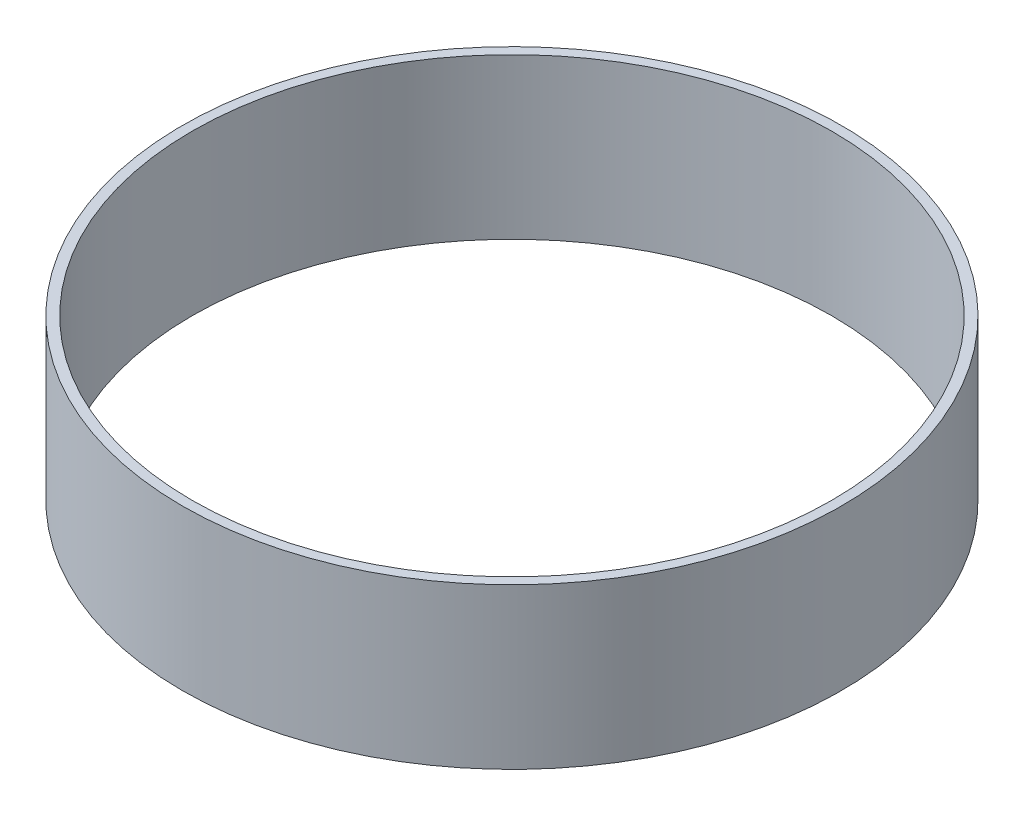
SolidWorks part; units mm, degrees
material "C-Glass Fiber"
ref_plane "Front Plane" through (0, 0, 0) normal (0, 0, 1) x (1, 0, 0)
ref_plane "Top Plane" through (0, 0, 0) normal (0, 1, 0) x (1, 0, 0)
ref_plane "Right Plane" through (0, 0, 0) normal (1, 0, 0) x (0, 0, -1)
sketch "Sketch1" plane through (0, 0, 0) normal (0, 1, 0) x (1, 0, 0)
  circle A0 centre (0, 0) radius 63.5
  circle A1 centre (0, 0) radius 65.4431
  dimension "D1" = 127
  dimension "D2" = 130.8862
extrude "Boss-Extrude2" add sketch "Sketch1" along normal blind 31.75
